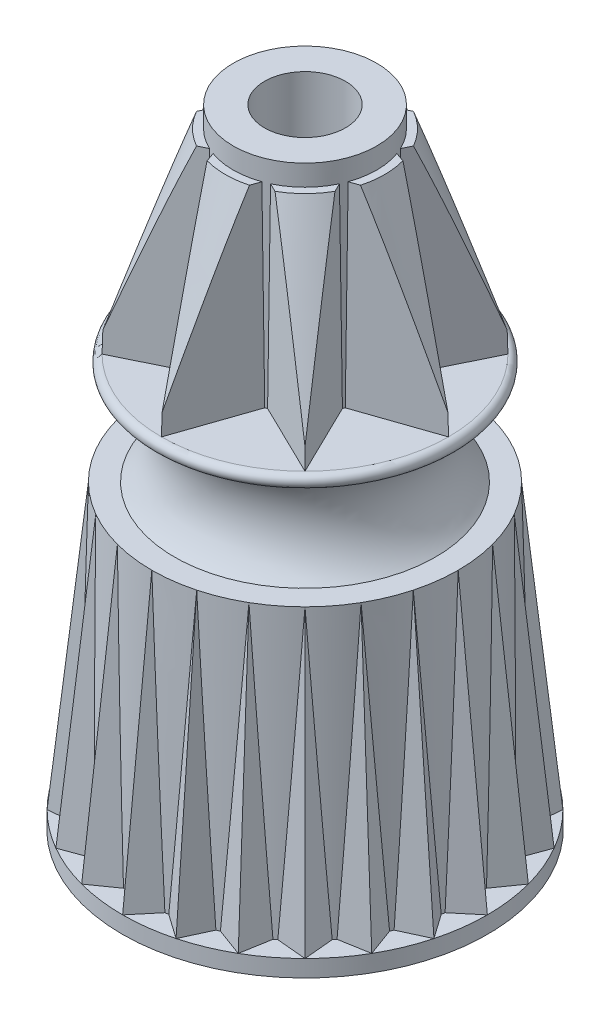
SolidWorks part; units mm, degrees
material "CA"
ref_plane "Front Plane" through (0, 0, 0) normal (0, 0, 1) x (1, 0, 0)
ref_plane "Top Plane" through (0, 0, 0) normal (0, 1, 0) x (1, 0, 0)
ref_plane "Right Plane" through (0, 0, 0) normal (1, 0, 0) x (0, 0, -1)
sketch "Sketch1" plane through (0, 0, 0) normal (0, 1, 0) x (1, 0, 0)
  circle A0 centre (0, 0) radius 8.89
  dimension "D1" = 17.78
extrude "Boss-Extrude1" add sketch "Sketch1" along normal blind 0.8128 draft 1
ref_plane "Plane1" through (0, 14.6304, 0) normal (0, 1, 0) x (1, 0, 0)
sketch "Sketch2" plane through (0, 14.6304, 0) normal (0, 1, 0) x (1, 0, 0)
  circle A0 centre (0, 0) radius 7.4549
  dimension "D1" = 14.9098
sketch "Sketch3" plane through (0, 0.8128, 0) normal (0, 1, 0) x (1, 0, 0)
  circle A0 centre (0, 0) radius 7.8105
  dimension "D1" = 15.621
loft "Loft1" add profiles "Sketch2", "Sketch3"
sketch "Sketch4" plane through (0, 0, 0) normal (1, 0, 0) x (0, 0, -1)
  line L0 (-7.4549, 14.6304) -> (-7.8105, 0.8128) construction
  line L1 (-7.4549, 14.6304) -> (-7.8105, 0.8128) construction
  line L2 (-8.8758, 0.8128) -> (-8.89, 0) construction
  line L3 (-8.8758, 0.8128) -> (-8.89, 0) construction
  line L4 (-8.8758, 0.8128) -> (-7.4549, 14.6304)
ref_plane "Plane2" through (0, 0.8128, 8.8758) normal (0, 0.9948, -0.1023) x (1, 0, 0)
sketch "Sketch5" plane through (0, 0.8128, 8.8758) normal (0, 0.9948, -0.1023) x (1, 0, 0)
  line L0 (0, 0) -> (0, 2.0328) construction
  line L1 (0, 0) -> (0, 1.0597) construction
  line L2 (0, 0) -> (1.2788, 1.524)
  line L3 (0, 0) -> (-1.2788, 1.524)
  line L4 (1.2788, 1.524) -> (-1.2788, 1.524)
  ellipse E0 centre (0, 8.8293) end of major axis (-8.8758, 8.8293) minor radius 8.8293 construction
  dimension "D1" = 80
  dimension "D2" = 1.524
sweep "Sweep1" add profiles "Sketch5" path "Sketch4"
pattern_circular "CirPattern1" count 24 over 360 about axis through (0, 0, 0) along (0, 1, 0) of "Sweep1"
sketch "Sketch7" plane through (0, 0, 0) normal (1, 0, 0) x (0, 0, -1)
  line L0 (0, 0) -> (0, 25.5262) construction
  line L1 (0, 0.8128) -> (0, 14.6304) construction
  line L2 (0, 20.0152) -> (6.985, 20.0152)
  line L3 (6.985, 19.3802) -> (6.35, 19.3802)
  line L4 (1.9295, 14.6304) -> (0, 14.6304) construction
  line L6 (16.7407, 14.6304) -> (0, 14.6304) construction
  line L7 (6.35, 14.6304) -> (0, 14.6304)
  line L8 (0, 14.6304) -> (0, 20.0152)
  arc A0 (6.985, 20.0152) -> (6.985, 19.3802) centre (6.985, 19.6977) cw
  arc A1 (6.35, 19.3802) -> (6.35, 14.6304) centre (8.6591, 17.0053) ccw
  dimension "D4" = 10.6934
  dimension "D1" = 12.7
  dimension "D2" = 0.635
  dimension "D3" = 0.635
  dimension "D5" = 4.7498
revolve "Revolve1" add sketch "Sketch7" angle 360 about L8
sketch "Sketch8" plane through (0, 20.0152, 0) normal (0, 1, 0) x (1, 0, 0)
  circle A0 centre (0, 0) radius 3.4925
  dimension "D1" = 6.985
extrude "Boss-Extrude2" add sketch "Sketch8" along a picked direction on the side of the normal offset from surface (10.5156 mm away) 30.5308
sketch "Sketch9" plane through (0, 30.5308, 0) normal (0, 1, 0) x (1, 0, 0)
  circle A0 centre (0, 0) radius 1.9685
  dimension "D1" = 3.937
extrude "Cut-Extrude1" cut sketch "Sketch9" against normal through all
sketch "Sketch10" plane through (0, 20.0152, 0) normal (0, 1, 0) x (1, 0, 0)
  line L0 (0, 0) -> (0, -9.673) construction
  line L1 (0, -6.985) -> (-1.5664, -2.436)
  line L2 (0, -6.985) -> (1.5664, -2.436)
  line L3 (-1.5664, -2.436) -> (1.5664, -2.436)
  circle A0 centre (0, 0) radius 6.985 construction
  dimension "D1" = 4.549
  dimension "D2" = 38
extrude "Boss-Extrude3" add sketch "Sketch10" along normal offset from surface 1.016 draft 0.5
pattern_circular "CirPattern2" count 8 over 360 about axis through (0, 0, 0) along (0, 1, 0) of "Boss-Extrude3"
sketch "Sketch11" plane through (0, 0, 0) normal (1, 0, 0) x (0, 0, -1)
  line L1 (3.4925, 29.5148) -> (3.4925, 30.5308) construction
  line L2 (6.7304, 29.5148) -> (6.985, 20.0152) construction
  line L3 (6.7304, 29.5148) -> (6.985, 20.0152) construction
  line L4 (3.4925, 29.5148) -> (6.9578, 21.0308) construction
  line L5 (6.9578, 21.0308) -> (7.4658, 21.0308)
  line L6 (7.4658, 21.0308) -> (7.4658, 30.5308)
  line L8 (3.4925, 29.5148) -> (3.8735, 29.5148)
  line L9 (1.4838, 29.5148) -> (4.7591, 29.5148) construction
  line L10 (3.8735, 29.5148) -> (6.9578, 21.0308)
  line L12 (3.4925, 29.5148) -> (3.4925, 30.5308)
  line L13 (3.4925, 30.5308) -> (7.4658, 30.5308)
  dimension "D1" = 1.016
  dimension "D2" = 0.508
  dimension "D3" = 0.381
revolve "Cut-Revolve1" cut sketch "Sketch11" angle 360 about axis through (0, 70.9399, 0) along (0, -1, 0)
sketch "Sketch12" plane through (0, 0, 0) normal (1, 0, 0) x (0, 0, -1)
  line L0 (0, 0) -> (0, 28.1928) construction
  line L1 (2.921, 0) -> (3.1941, 15.6464)
  line L2 (3.1941, 15.6464) -> (4.5495, 15.6464)
  line L4 (-8.89, 0) -> (8.89, 0) construction
  line L5 (6.2319, 14.2909) -> (6.6263, 2.9972) construction
  line L6 (2.921, 0) -> (2.921, -2.54)
  line L7 (2.921, -2.54) -> (6.731, -2.54)
  line L8 (6.731, 0) -> (6.731, -2.54)
  line L9 (6.4484, 2.9972) -> (6.491, 1.778)
  line L10 (5.8897, 13.902) -> (6.2705, 2.9972)
  line L11 (6.491, 1.778) -> (6.6689, 1.778)
  line L12 (6.2705, 2.9972) -> (6.4484, 2.9972)
  line L13 (6.6689, 1.778) -> (6.731, 0)
  line L14 (6.0543, 14.2847) -> (6.5533, -0.0062) construction
  line L15 (5.8766, 14.2785) -> (6.3756, -0.0124) construction
  line L16 (5.6417, 13.902) -> (5.8897, 13.902)
  line L17 (6.2319, 14.2909) -> (6.731, 0) construction
  circle A0 centre (0, 0) radius 2.921 construction
  arc A1 (6.35, 19.3802) -> (6.35, 14.6304) centre (8.6591, 17.0053) ccw construction
  arc A2 (6.35, 19.3802) -> (6.35, 14.6304) centre (8.6591, 17.0053) ccw construction
  arc A3 (4.5495, 15.6464) -> (5.6417, 13.902) centre (8.6591, 17.0053) ccw
  circle A4 centre (0, 0) radius 6.731 construction
  arc A5 (5.6417, 20.1086) -> (5.6417, 13.902) centre (8.6591, 17.0053) ccw construction
  dimension "D1" = 5.842
  dimension "D6" = 13.462
  dimension "D3" = 1
  dimension "D4" = 15.6464
  dimension "D5" = 2
  dimension "D7" = 2.54
  dimension "D10" = 1.778
  dimension "D11" = 2.9972
  dimension "D2" = 1.016
  dimension "D8" = 0.1778
  dimension "D9" = 0.1778
revolve "Cut-Revolve2" cut sketch "Sketch12" angle 360 about L0
fillet "Fillet1" radius 0.762 1 edges at (0, 0, -6.731)
sketch "Sketch13" plane through (0, 1.778, 0) normal (0, -1, 0) x (1, 0, 0)
  line L0 (0, -6.491) -> (0, -2.4467)
  line L1 (0, 2.4467) -> (0, 6.491)
  circle A0 centre (0, 0) radius 6.491 construction
  circle A1 centre (0, 0) radius 2.4467 construction
rib "Rib1" sketch "Sketch13" sketch "Sketch13" thickness 1.016 parameters "D1"=1.016, "D3"=1
fillet "Fillet2" radius 0.508 8 edges at (0.508, 1.778, 4.6895) (-0.6093, 7.5791, 2.9919) (-0.508, 1.778, 4.6895) (0.6093, 7.5791, 2.9919) (-0.508, 1.778, -4.6895) (0.508, 1.778, -4.6895)
